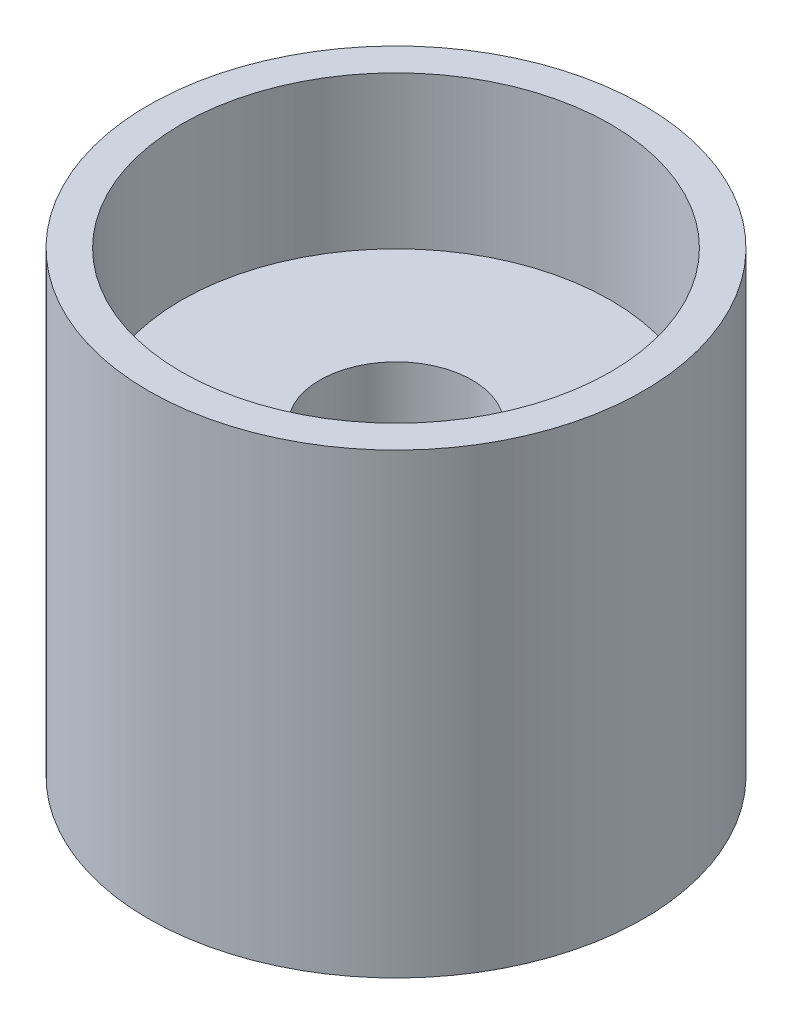
SolidWorks part; units mm, degrees
ref_plane "Front Plane" through (0, 0, 0) normal (0, 0, 1) x (1, 0, 0)
ref_plane "Top Plane" through (0, 0, 0) normal (0, 1, 0) x (1, 0, 0)
ref_plane "Right Plane" through (0, 0, 0) normal (1, 0, 0) x (0, 0, -1)
sketch "Sketch2" plane through (0, 0, 0) normal (0, 0, 1) x (1, 0, 0)
  line L2 (-3.175, -6.35) -> (-8.9408, -6.35)
  line L3 (-8.9408, -6.35) -> (-8.9408, 0)
  line L4 (-8.9408, 0) -> (-10.3124, 0)
  line L5 (-10.3124, 0) -> (-10.3124, -19.05)
  line L6 (-10.3124, -19.05) -> (-3.175, -19.05)
  line L9 (-3.175, -19.05) -> (-3.175, -6.35)
  line L10 (0, 0) -> (0, -4.4266) construction
  point P1 (-3.175, -3.175)
  point P10 (-3.3532, -3.175)
  dimension "D2" = 3.175
  dimension "D3" = 10.3124
  dimension "D5" = 8.9408
  dimension "D7" = 6.35
  dimension "D10" = 19.05
revolve "Revolve1" add sketch "Sketch2" angle 360 about L10
